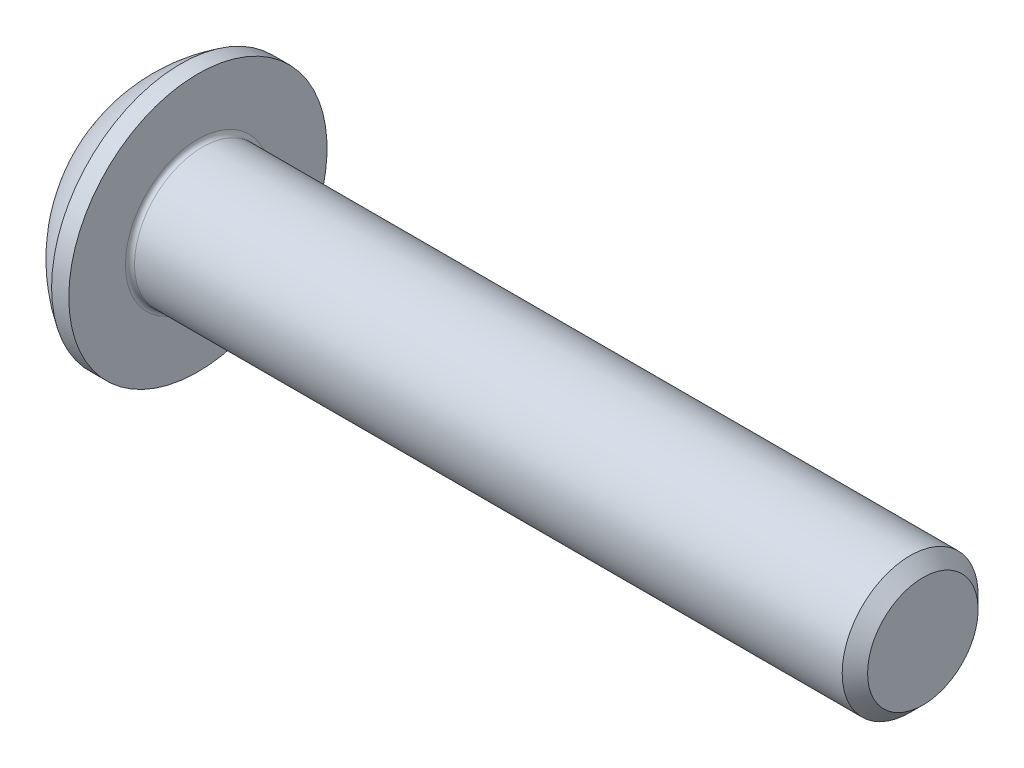
SolidWorks part; units mm, degrees
ref_plane "Plane1" through (0, 0, 0) normal (0, 0, 1) x (1, 0, 0)
ref_plane "Plane2" through (0, 0, 0) normal (0, 1, 0) x (1, 0, 0)
ref_plane "Plane3" through (0, 0, 0) normal (1, 0, 0) x (0, 0, -1)
sketch "BodySke" plane through (0, 0, 0) normal (0, 0, 1) x (1, 0, 0)
  line L0 (17.65, 0) -> (17.65, 1.2195)
  line L1 (17.3695, 1.5) -> (1.65, 1.5)
  line L2 (1.65, 1.5) -> (1.65, 2.85)
  line L3 (1.65, 2.85) -> (1.27, 2.85)
  line L4 (0, 0) -> (101.6, 0) construction
  line L5 (1.65, -2.85) -> (1.27, -2.85) construction
  line L6 (55.6768, -1.5) -> (1.65, -1.5) construction
  line L7 (17.65, 0) -> (0, 0)
  line L8 (0, 1.425) -> (0, -1.425) construction
  line L9 (0, 0) -> (0, 1.425)
  line L10 (17.65, 1.2195) -> (17.3695, 1.5)
  line L11 (17.65, -1.2195) -> (17.3695, -1.5) construction
  line L12 (2.15, 9.525) -> (2.15, -1.5) construction
  line L13 (11.65, 9.525) -> (11.65, -1.5) construction
  arc A1 (0, 1.425) -> (1.27, 2.85) centre (3.0334, 0) cw
  dimension "D1" = 2.85
  dimension "Diameter" = 3
  dimension "Length" = 16
  dimension "Head_dia" = 5.7
  dimension "Head_ht" = 1.65
  dimension "Head_side_ht" = 0.38
  dimension "Minor_dia" = 2.439
  dimension "Body_ch_ang" = 45
  dimension "Advance" = 0.5
  dimension "Thread_nom" = 6
revolve "BaseBody" add sketch "BodySke" angle 360 about L4
cosmetic thread "ThreadCosmetic" [suppressed] parameters "Thread_length"=6, "Thread_minor"=2.439
fillet "Fillet1" radius 0.1 1 edges at (1.65, 0, 1.5)
sketch "Sketch2" plane through (0, 0, 0) normal (0, 0, 1) x (1, 0, 0)
  line L0 (0, 1) -> (1.04, 1)
  line L1 (1.04, 1) -> (1.6174, 0)
  line L3 (1.6174, 0) -> (0, 0)
  line L4 (0, 0) -> (0, 1)
  line L5 (0, -1) -> (1.04, -1) construction
  line L6 (0, 0) -> (47.625, 0) construction
  dimension "D2" = 60
  dimension "PreBroach_depth" = 1.04
  dimension "PreBroach_dia" = 2
revolve "PreBroach" cut sketch "Sketch2" angle 360 about L6
sketch "Sketch3" plane through (0, 0, 0) normal (1, 0, 0) x (0, 0, -1)
  line L0 (-1, -0.5774) -> (-1, 0.5774)
  line L1 (-1, 0.5774) -> (0, 1.1547)
  line L2 (0, 1.1547) -> (1, 0.5774)
  line L3 (1, 0.5774) -> (1, -0.5774)
  line L4 (1, -0.5774) -> (0, -1.1547)
  line L5 (0, -1.1547) -> (-1, -0.5774)
  dimension "D1" = 1
  dimension "D2" = 1
  dimension "D3" = 2
  dimension "Hex_size" = 2
extrude "Hex" cut sketch "Sketch3" along normal blind 1.04
sketch "ThdSchSke" plane through (0, 0, 0) normal (0, 0, 1) x (1, 0, 0)
  line L0 (11.65, -1.2195) -> (11.4536, -1.5)
  line L1 (11.65, -1.2195) -> (11.8464, -1.5)
  line L2 (11.8464, -1.5) -> (11.8464, -1.875)
  line L3 (-3.175, 0) -> (5.1513, 0) construction
  line L5 (11.8464, -1.875) -> (11.4536, -1.875)
  line L6 (11.4536, -1.875) -> (11.4536, -1.5)
  dimension "Thread_minor" = 2.439
  dimension "Diameter" = 3
  dimension "Start" = 11.65
  dimension "SideAngle" = 55
  dimension "VeeAngle" = 70
  dimension "Overcut" = 3.75
revolve "ThreadSchematic" [suppressed] cut sketch "ThdSchSke" angle 360 about L3
pattern_linear "ThdSchPat" [suppressed]
equation "\"D1@BodySke\" = \"Head_dia@BodySke\" * .5"
equation "\"Thread_minor@ThreadCosmetic\" = \"Minor_dia@BodySke\""
equation "\"D1@Sketch3\" = \"Hex_size@Sketch3\" / 2"
equation "\"D2@Sketch3\" = \"D1@Sketch3\""
equation "\"D3@Sketch3\" = \"Hex_size@Sketch3\""
equation "\"Thread_length@ThreadCosmetic\" = ((sgn( (\"Length@BodySke\" - \"Advance@BodySke\" * 2.0) - \"Thread_nom@BodySke\" )-1)*( (\"Length@BodySke\" - \"Advance@BodySke\" * 2.0) - \"Thread_nom@BodySke\" ))/-2+ \"Thread_nom@BodySke\""
equation "\"Thread_minor@ThdSchSke\" = \"Minor_dia@BodySke\""
equation "\"Diameter@ThdSchSke\" = \"Diameter@BodySke\""
equation "\"Overcut@ThdSchSke\" = \"Diameter@BodySke\" * 1.25"
equation "\"Start@ThdSchSke\" = \"Head_ht@BodySke\" + \"Length@BodySke\" - \"Thread_length@ThreadCosmetic\"  '---Non-countersunk---"
equation "\"Num_threads@ThdSchPat\" = int( \"Thread_length@ThreadCosmetic\" / \"Advance@BodySke\" + 0.999 )  + 1"
equation "\"Advance@ThdSchPat\" = \"Thread_length@ThreadCosmetic\" /  (\"Num_threads@ThdSchPat\" - 1) 'relax it"
equation "\"Num_threads@ThdSchPat\" = \"Num_threads@ThdSchPat\" - sgn( \"Num_threads@ThdSchPat\" - 1) '---chamfered tips only---"
